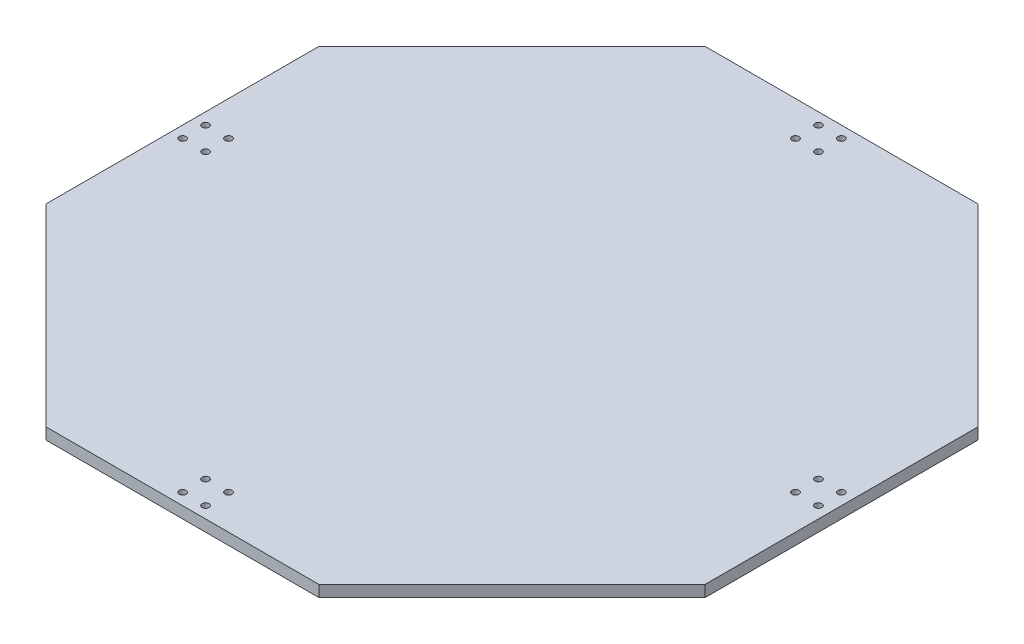
SolidWorks part; units mm, degrees
material "6061 합금"
ref_plane "정면" through (0, 0, 0) normal (0, 0, 1) x (1, 0, 0)
ref_plane "윗면" through (0, 0, 0) normal (0, 1, 0) x (1, 0, 0)
ref_plane "우측면" through (0, 0, 0) normal (1, 0, 0) x (0, 0, -1)
sketch "스케치1" plane through (0, 0, 0) normal (0, 1, 0) x (1, 0, 0)
  line L0 (0, 278.2405) -> (0, -303.6506) construction
  line L1 (-342.3832, 0) -> (358.9353, 0) construction
  line L3 (59.4811, -143.6) -> (143.6, -59.4811)
  line L4 (143.6, -59.4811) -> (143.6, 59.4811)
  line L5 (143.6, 59.4811) -> (59.4811, 143.6)
  line L6 (59.4811, 143.6) -> (-59.4811, 143.6)
  line L7 (-59.4811, 143.6) -> (-143.6, 59.4811)
  line L8 (-143.6, 59.4811) -> (-143.6, -59.4811)
  line L9 (-143.6, -59.4811) -> (-59.4811, -143.6)
  line L10 (-59.4811, -143.6) -> (59.4811, -143.6)
  circle A0 centre (0, 0) radius 143.6 construction
  circle A1 centre (-5, 138.54) radius 1.5
  circle A2 centre (-5, 128.54) radius 1.5
  circle A7 centre (5, 128.54) radius 1.5
  circle A8 centre (5, 138.54) radius 1.5
  circle A9 centre (138.54, 5) radius 1.5
  circle A10 centre (128.54, 5) radius 1.5
  circle A15 centre (128.54, -5) radius 1.5
  circle A16 centre (138.54, -5) radius 1.5
  circle A17 centre (5, -138.54) radius 1.5
  circle A18 centre (5, -128.54) radius 1.5
  circle A23 centre (-5, -128.54) radius 1.5
  circle A24 centre (-5, -138.54) radius 1.5
  circle A25 centre (-138.54, -5) radius 1.5
  circle A26 centre (-128.54, -5) radius 1.5
  circle A31 centre (-128.54, 5) radius 1.5
  circle A32 centre (-138.54, 5) radius 1.5
  point P82 (0, 0)
  point P115 (0, -46.8105)
  dimension "D2" = 3
  dimension "D5" = 3
  dimension "D1" = 287.2
  dimension "D3" = 5
  dimension "D4" = 5.06
  dimension "D6" = 10
  dimension "D11" = 4
extrude "보스-돌출1" add sketch "스케치1" along normal blind 5
